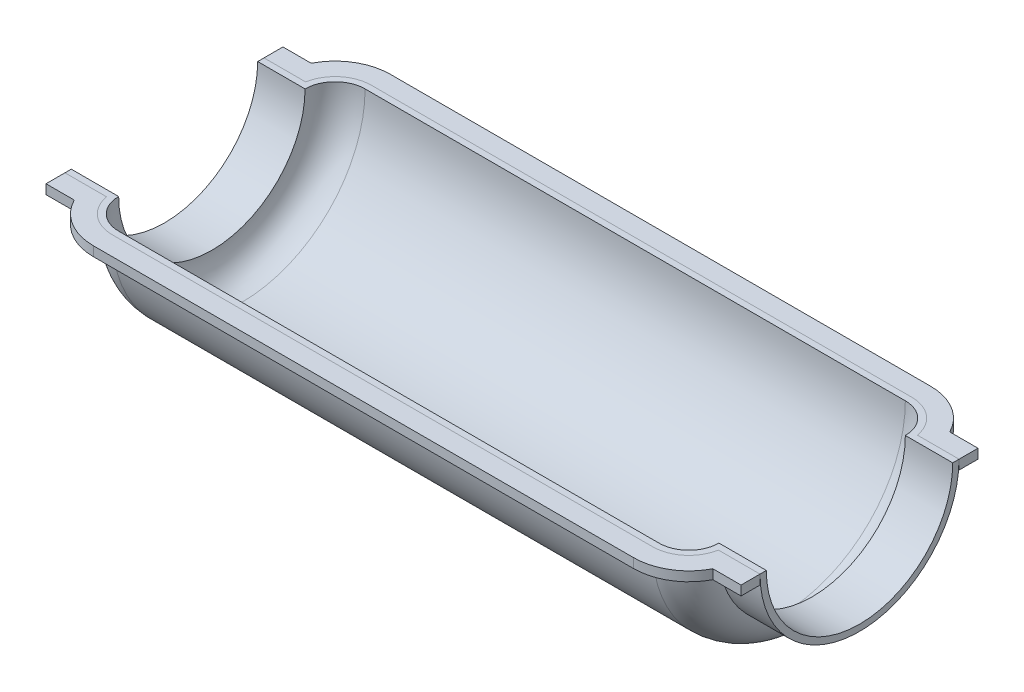
SolidWorks part; units mm, degrees
ref_plane "Front Plane" through (0, 0, 0) normal (0, 0, 1) x (1, 0, 0)
ref_plane "Top Plane" through (0, 0, 0) normal (0, 1, 0) x (1, 0, 0)
ref_plane "Right Plane" through (0, 0, 0) normal (1, 0, 0) x (0, 0, -1)
sketch "Sketch1" plane through (0, 0, 0) normal (0, 1, 0) x (1, 0, 0)
  line L0 (-110, 29.5) -> (-95, 29.5)
  line L1 (-85.5, 39) -> (85.5, 39)
  line L2 (95, 29.5) -> (110, 29.5)
  line L3 (0, 0) -> (-26985.5982, 0) construction
  line L4 (0, 0) -> (0, 26985.5982) construction
  line L5 (-110, 31.5) -> (-96.8248, 31.5)
  line L6 (-85.5, 41) -> (85.5, 41)
  line L7 (96.8248, 31.5) -> (110, 31.5)
  line L8 (-110, 31.5) -> (-110, 29.5)
  line L9 (110, 31.5) -> (110, 29.5)
  arc A0 (-95, 29.5) -> (-85.5, 39) centre (-85.5, 29.5) cw
  arc A1 (85.5, 39) -> (95, 29.5) centre (85.5, 29.5) cw
  arc A2 (-96.8248, 31.5) -> (-85.5, 41) centre (-85.5, 29.5) cw
  arc A3 (85.5, 41) -> (96.8248, 31.5) centre (85.5, 29.5) cw
  dimension "D3" = 29.5
  dimension "D1" = 15
  dimension "D2" = 220
  dimension "D4" = 39
  dimension "D5" = 2
revolve "Revolve1" add sketch "Sketch1" angle 180 about L3
sketch "Sketch2" plane through (0, 0, 0) normal (0, 1, 0) x (1, 0, 0)
  line L8 (-96.8248, 31.5) -> (-110, 31.5) construction
  line L9 (-96.8248, 31.5) -> (-110, 31.5)
  line L10 (110, 31.5) -> (96.8248, 31.5) construction
  line L11 (110, 37.5) -> (101.0644, 37.5)
  line L12 (-101.0644, 37.5) -> (-110, 37.5)
  line L13 (85.5, 47) -> (-85.5, 47)
  line L14 (110, 37.5) -> (101.0644, 37.5)
  line L15 (-101.0644, 37.5) -> (-110, 37.5)
  line L16 (85.5, 47) -> (-85.5, 47)
  line L17 (85.5, 41) -> (-85.5, 41) construction
  line L18 (110, 31.5) -> (96.8248, 31.5)
  line L19 (85.5, 41) -> (-85.5, 41)
  line L20 (-110, 37.5) -> (-110, 31.5)
  line L22 (0, 0) -> (-50000, 0) construction
  line L23 (110, 37.5) -> (110, 31.5)
  line L24 (110, -37.5) -> (110, -31.5)
  line L25 (-110, -37.5) -> (-110, -31.5)
  line L26 (85.5, -41) -> (-85.5, -41)
  line L27 (110, -31.5) -> (96.8248, -31.5)
  line L28 (85.5, -47) -> (-85.5, -47)
  line L29 (-101.0644, -37.5) -> (-110, -37.5)
  line L30 (110, -37.5) -> (101.0644, -37.5)
  line L31 (-96.8248, -31.5) -> (-110, -31.5)
  arc A7 (96.8248, 31.5) -> (85.5, 41) centre (85.5, 29.5) ccw construction
  arc A8 (-85.5, 41) -> (-96.8248, 31.5) centre (-85.5, 29.5) ccw construction
  arc A9 (101.0644, 37.5) -> (85.5, 47) centre (85.5, 29.5) ccw
  arc A10 (-85.5, 47) -> (-101.0644, 37.5) centre (-85.5, 29.5) ccw
  arc A11 (101.0644, 37.5) -> (85.5, 47) centre (85.5, 29.5) ccw
  arc A12 (-85.5, 47) -> (-101.0644, 37.5) centre (-85.5, 29.5) ccw
  arc A13 (96.8248, 31.5) -> (85.5, 41) centre (85.5, 29.5) ccw
  arc A14 (-85.5, 41) -> (-96.8248, 31.5) centre (-85.5, 29.5) ccw
  arc A15 (-85.5, -41) -> (-96.8248, -31.5) centre (-85.5, -29.5) cw
  arc A16 (96.8248, -31.5) -> (85.5, -41) centre (85.5, -29.5) cw
  arc A17 (-85.5, -47) -> (-101.0644, -37.5) centre (-85.5, -29.5) cw
  arc A18 (101.0644, -37.5) -> (85.5, -47) centre (85.5, -29.5) cw
  dimension "D1" = 6
extrude "Boss-Extrude1" add sketch "Sketch2" against normal blind 3 separate body
